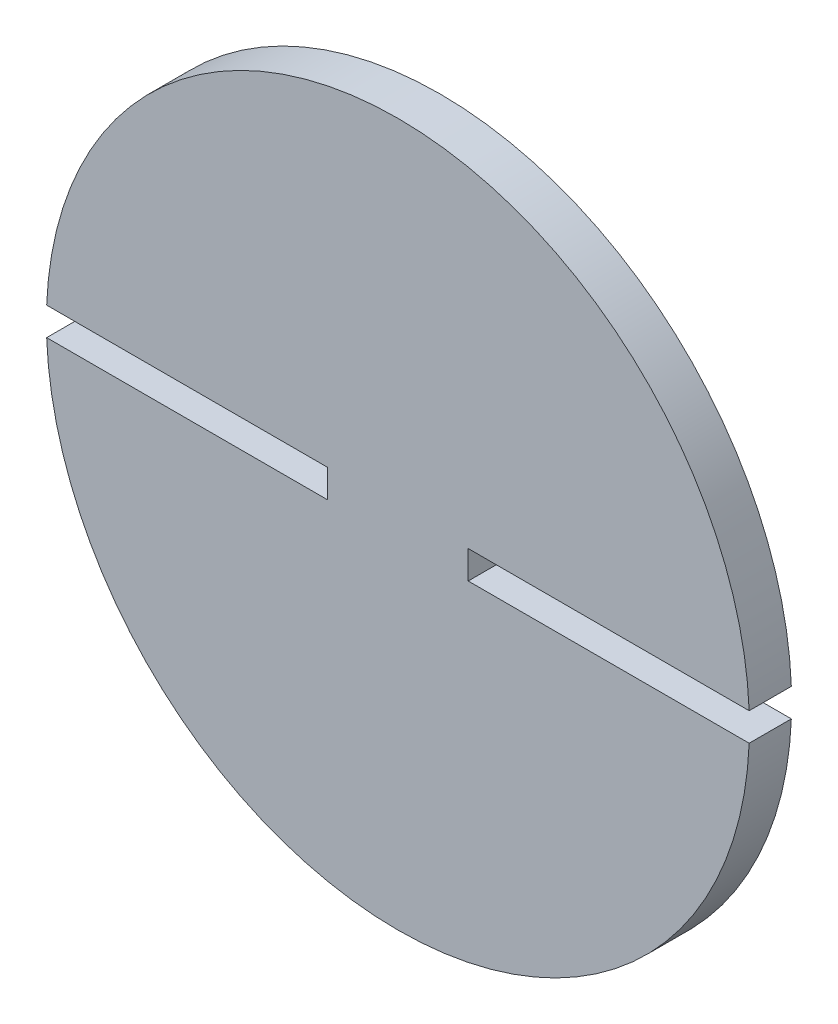
SolidWorks part; units mm, degrees
ref_plane "Front Plane" through (0, 0, 0) normal (0, 0, 1) x (1, 0, 0)
ref_plane "Top Plane" through (0, 0, 0) normal (0, 1, 0) x (1, 0, 0)
ref_plane "Right Plane" through (0, 0, 0) normal (1, 0, 0) x (0, 0, -1)
sketch "Sketch1" plane through (0, 0, 0) normal (0, 0, 1) x (1, 0, 0)
  circle A0 centre (0, 0) radius 25
extrude "Boss-Extrude1" add sketch "Sketch1" along normal blind 3
sketch "Sketch2" plane through (0, 0, 0) normal (0, 0, -1) x (-1, 0, 0)
  line L0 (-5, 0) -> (-31.7402, 0) construction
  line L1 (-5, -5) -> (5, -5)
  line L2 (-5, -5) -> (-5, 5)
  line L3 (-5, 5) -> (5, 5)
  line L4 (5, -5) -> (5, 5)
  line L5 (-5, -5) -> (5, 5) construction
  line L6 (-5, 5) -> (5, -5) construction
  line L7 (5, 0) -> (28.8874, 0) construction
  line L8 (-15.7044, 0) -> (-15.7044, 1) construction
  line L9 (-14.0829, 0) -> (-14.0829, -1) construction
  line L10 (14.5877, 0) -> (14.5877, 1) construction
  line L11 (13.7549, 0) -> (13.7549, -1) construction
  line L12 (-5, 1) -> (-24.98, 1)
  line L13 (-5, -1) -> (-24.98, -1)
  line L14 (5, 1) -> (24.98, 1)
  line L15 (5, -1) -> (24.98, -1)
  circle A0 centre (0, 0) radius 25 construction
  arc A1 (-24.98, -1) -> (-24.98, 1) centre (0, 0) cw
  arc A2 (24.98, -1) -> (24.98, 1) centre (0, 0) ccw
  point P0 (0, 0)
  circle M3 centre (0, 0) radius 25
extrude "Cut-Extrude1" cut sketch "Sketch2" against normal blind 3 contours L13 L2 L12 M3 | L4 L15 L14 M3
